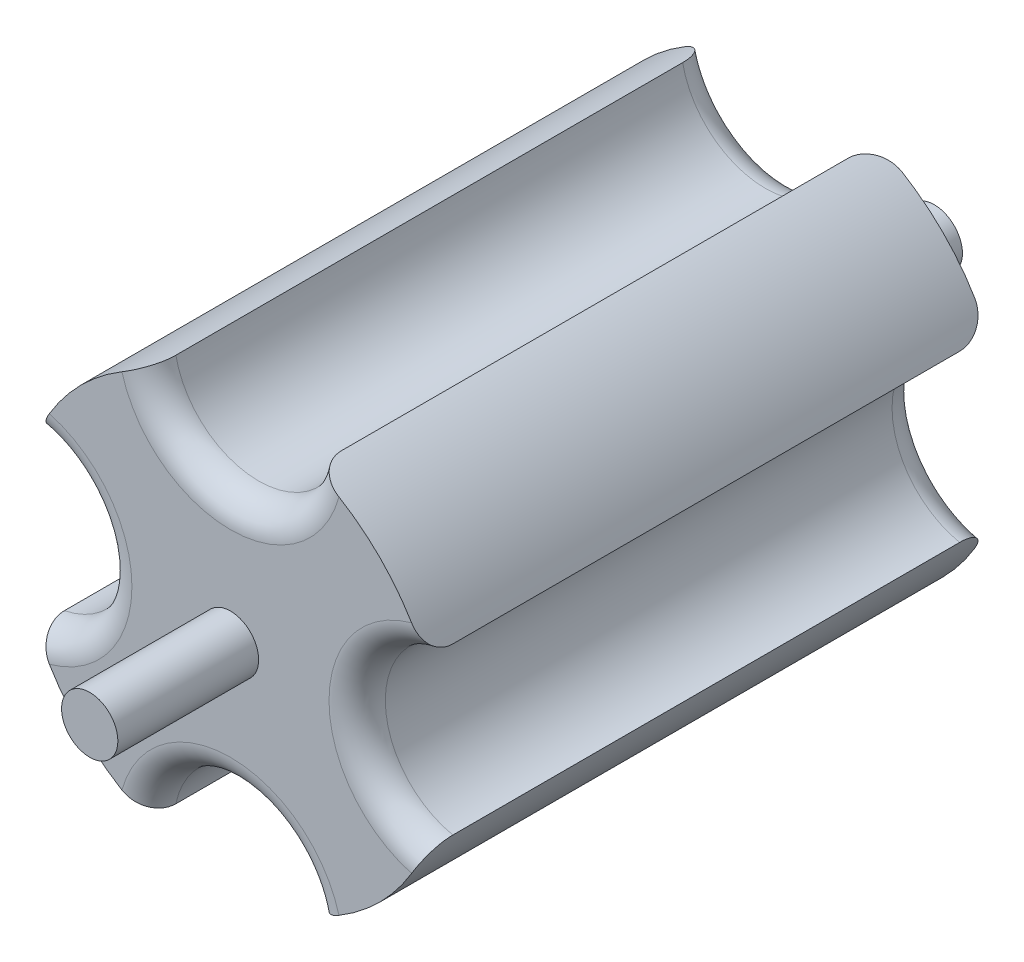
SolidWorks part; units mm, degrees
ref_plane "Front Plane" through (0, 0, 0) normal (0, 0, 1) x (1, 0, 0)
ref_plane "Top Plane" through (0, 0, 0) normal (0, 1, 0) x (1, 0, 0)
ref_plane "Right Plane" through (0, 0, 0) normal (1, 0, 0) x (0, 0, -1)
sketch "Sketch2" plane through (0, 0, 0) normal (0, 0, 1) x (1, 0, 0)
  circle A0 centre (0, 0) radius 19.05
  dimension "D1" = 38.1
extrude "Boss-Extrude1" add sketch "Sketch2" along normal blind 50.8
sketch "Sketch5" plane through (0, 0, 50.8) normal (0, 0, 1) x (1, 0, 0)
  circle A0 centre (0, 19.05) radius 7.62
  circle A1 centre (0, 0) radius 19.05 construction
  circle A2 centre (19.05, 0) radius 7.62
  circle A3 centre (0, -19.05) radius 7.62
  circle A4 centre (-19.05, 0) radius 7.62
  point P13 (0, 0)
  dimension "D1" = 4
extrude "Cut-Extrude2" cut sketch "Sketch5" against normal through all
sketch "Sketch6" plane through (0, 0, 50.8) normal (0, 0, 1) x (1, 0, 0)
  circle A0 centre (0, 0) radius 2.54
extrude "Boss-Extrude2" add sketch "Sketch6" along normal blind 12.7
sketch "Sketch7" plane through (0, 0, 0) normal (0, 0, -1) x (-1, 0, 0)
  circle A0 centre (0, 0) radius 2.54
extrude "Boss-Extrude3" add sketch "Sketch7" along normal blind 12.7
fillet "Fillet1" radius 2.54 8 edges at (11.43, 0, 50.8) (0, 11.43, 50.8) (0, -11.43, 50.8) (-11.43, 0, 50.8) (0, -11.43, 0) (-11.43, 0, 0) (11.43, 0, 0) (0, 11.43, 0)
